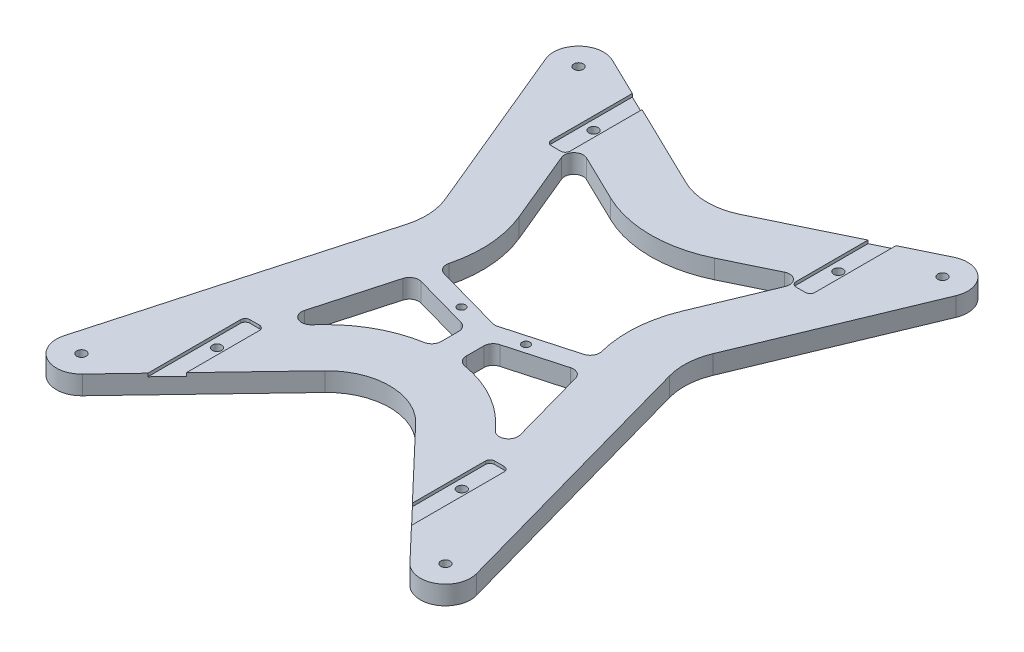
SolidWorks part; units mm, degrees
material "1060 Alloy"
ref_plane "Front Plane" through (0, 0, 0) normal (0, 0, 1) x (1, 0, 0)
ref_plane "Top Plane" through (0, 0, 0) normal (0, 1, 0) x (1, 0, 0)
ref_plane "Right Plane" through (0, 0, 0) normal (1, 0, 0) x (0, 0, -1)
sketch "Sketch1" plane through (0, 0, 0) normal (0, 1, 0) x (1, 0, 0)
  line L0 (-54.4954, 86.3958) -> (0, 60)
  line L1 (0, 60) -> (54.4954, 86.3958)
  line L2 (65.3716, 76.1292) -> (40, 15)
  line L3 (40, 15) -> (65.6883, -77.0455)
  line L4 (52.194, -84.7177) -> (0, -30)
  line L5 (0, -30) -> (-52.194, -84.7177)
  line L6 (-65.6883, -77.0455) -> (-40, 15)
  line L7 (-40, 15) -> (-65.3716, 76.1292)
  line L8 (-68.5894, 68.5894) -> (68.5894, -68.5894) construction
  line L9 (-42, 75) -> (-36, 75) construction
  line L10 (-42, 75) -> (-42, 55) construction
  line L11 (-42, 55) -> (-36, 55) construction
  line L12 (-36, 75) -> (-36, 55) construction
  line L13 (-42, 75) -> (-36, 55) construction
  line L14 (-42, 55) -> (-36, 75) construction
  line L15 (36, 75) -> (42, 75) construction
  line L16 (36, 75) -> (36, 55) construction
  line L17 (36, 55) -> (42, 55) construction
  line L18 (42, 75) -> (42, 55) construction
  line L19 (36, 75) -> (42, 55) construction
  line L20 (36, 55) -> (42, 75) construction
  line L21 (36, -45) -> (42, -45) construction
  line L22 (36, -45) -> (36, -65) construction
  line L23 (36, -65) -> (42, -65) construction
  line L24 (42, -45) -> (42, -65) construction
  line L25 (36, -45) -> (42, -65) construction
  line L26 (36, -65) -> (42, -45) construction
  line L27 (-42, -45) -> (-36, -45) construction
  line L28 (-42, -45) -> (-42, -65) construction
  line L29 (-42, -65) -> (-36, -65) construction
  line L30 (-36, -45) -> (-36, -65) construction
  line L31 (-42, -45) -> (-36, -65) construction
  line L32 (-42, -65) -> (-36, -45) construction
  line L33 (97, 40.1787) -> (40.1787, 97) construction
  line L34 (40.1787, 97) -> (-40.1787, 97) construction
  line L35 (-40.1787, 97) -> (-97, 40.1787) construction
  line L36 (-97, 40.1787) -> (-97, -40.1787) construction
  line L37 (-97, -40.1787) -> (-40.1787, -97) construction
  line L38 (-40.1787, -97) -> (40.1787, -97) construction
  line L39 (40.1787, -97) -> (97, -40.1787) construction
  line L40 (97, -40.1787) -> (97, 40.1787) construction
  line L41 (68.5894, 68.5894) -> (-68.5894, -68.5894) construction
  circle A0 centre (-57.9828, 79.196) radius 1.5
  circle A1 centre (57.9828, 79.196) radius 1.5
  circle A2 centre (-57.9828, -79.196) radius 1.5
  circle A3 centre (57.9828, -79.196) radius 1.5
  arc A4 (-54.4954, 86.3958) -> (-65.3716, 76.1292) centre (-57.9828, 79.196) ccw
  arc A5 (54.4954, 86.3958) -> (65.3716, 76.1292) centre (57.9828, 79.196) cw
  arc A6 (-65.6883, -77.0455) -> (-52.194, -84.7177) centre (-57.9828, -79.196) ccw
  arc A7 (65.6883, -77.0455) -> (52.194, -84.7177) centre (57.9828, -79.196) cw
  circle A8 centre (0, 0) radius 97 construction
  circle A9 centre (-39, 65) radius 1.5
  circle A10 centre (39, 65) radius 1.5
  circle A11 centre (39, -55) radius 1.5
  circle A12 centre (-39, -55) radius 1.5
  ellipse E0 centre (0, 15) end of major axis (0, 60) minor radius 40 construction
  dimension "D5" = 3
  dimension "D6" = 45
  dimension "D7" = 8
  dimension "D12" = 3
  dimension "D3" = 15
  dimension "D4" = 15
  dimension "D8" = 120
  dimension "D9" = 78
  dimension "D10" = 15
  dimension "D11" = 55
  dimension "D13" = 40
  dimension "D14" = 39
  dimension "D15" = 20
  dimension "D16" = 6
  dimension "D17" = 97
  dimension "D18" = 15
extrude "Boss-Extrude1" add sketch "Sketch1" along normal blind 6
fillet "Fillet1" radius 20 4 edges at (0, 3, -60) (-40, 3, -15) (0, 3, 30) (40, 3, -15)
sketch "Sketch2" plane through (0, 6, 0) normal (0, 1, 0) x (1, 0, 0)
  line L44 (-38.6591, 58.7249) -> (-26.025, 28.2848)
  line L45 (-24.5208, 3.5031) -> (-37.5911, -43.3302)
  line L46 (-37.5911, -43.3302) -> (-27.4967, -32.7477)
  line L47 (27.4967, -32.7477) -> (37.5911, -43.3302)
  line L48 (37.5911, -43.3302) -> (24.5208, 3.5031)
  line L49 (26.025, 28.2848) -> (38.6591, 58.7249)
  line L50 (38.6591, 58.7249) -> (16.5651, 48.0232)
  line L51 (-16.5651, 48.0232) -> (-38.6591, 58.7249)
  line L52 (-38.6591, 58.7249) -> (-26.025, 28.2848)
  line L53 (-24.5208, 3.5031) -> (-37.5911, -43.3302)
  line L54 (-37.5911, -43.3302) -> (-27.4967, -32.7477)
  line L55 (27.4967, -32.7477) -> (37.5911, -43.3302)
  line L56 (37.5911, -43.3302) -> (24.5208, 3.5031)
  line L57 (26.025, 28.2848) -> (38.6591, 58.7249)
  line L58 (38.6591, 58.7249) -> (16.5651, 48.0232)
  line L59 (-16.5651, 48.0232) -> (-38.6591, 58.7249)
  arc A40 (-24.5208, 3.5031) -> (-26.025, 28.2848) centre (-61.1221, 13.7179) ccw
  arc A41 (27.4967, -32.7477) -> (-27.4967, -32.7477) centre (0, -58.9762) ccw
  arc A42 (26.025, 28.2848) -> (24.5208, 3.5031) centre (61.1221, 13.7179) ccw
  arc A43 (-16.5651, 48.0232) -> (16.5651, 48.0232) centre (0, 82.2226) ccw
  arc A44 (-24.5208, 3.5031) -> (-26.025, 28.2848) centre (-61.1221, 13.7179) ccw
  arc A45 (27.4967, -32.7477) -> (-27.4967, -32.7477) centre (0, -58.9762) ccw
  arc A46 (26.025, 28.2848) -> (24.5208, 3.5031) centre (61.1221, 13.7179) ccw
  arc A47 (-16.5651, 48.0232) -> (16.5651, 48.0232) centre (0, 82.2226) ccw
  dimension "D1" = 18
extrude "Cut-Extrude1" cut sketch "Sketch2" against normal up to next
sketch "Sketch5" plane through (0, 6, 0) normal (0, 1, 0) x (1, 0, 0)
  line L0 (-25.1032, 1.416) -> (0, -5.5899)
  line L1 (-12.94, -8.43) -> (12.94, -8.43) construction
  line L2 (-12.94, -8.43) -> (-12.94, 8.43) construction
  line L3 (-12.94, 8.43) -> (12.94, 8.43) construction
  line L4 (12.94, -8.43) -> (12.94, 8.43) construction
  line L5 (-12.94, -8.43) -> (12.94, 8.43) construction
  line L6 (-12.94, 8.43) -> (12.94, -8.43) construction
  line L7 (-24.5208, 3.5031) -> (-37.5911, -43.3302) construction
  line L8 (0, -5.5899) -> (25.1032, 1.416)
  line L9 (37.5911, -43.3302) -> (24.5208, 3.5031) construction
  line L10 (25.1032, 1.416) -> (26.7161, -4.3632)
  line L11 (26.7161, -4.3632) -> (4, -10.7029)
  line L12 (4, -10.7029) -> (4, -21.1873)
  line L13 (-4, -21.1873) -> (-4, -10.7029)
  line L14 (-4, -10.7029) -> (-26.7161, -4.3632)
  line L15 (-26.7161, -4.3632) -> (-25.1032, 1.416)
  circle A0 centre (-10.3, -5.83) radius 1.25
  circle A1 centre (10.3, -5.83) radius 1.25
  arc A2 (27.4967, -32.7477) -> (-27.4967, -32.7477) centre (0, -58.9762) ccw construction
  arc A3 (4, -21.1873) -> (-4, -21.1873) centre (0, -58.9762) ccw
  point P0 (0, 0)
  dimension "D3" = 2.5
  dimension "D1" = 16.86
  dimension "D2" = 25.88
  dimension "D4" = 20.6
  dimension "D5" = 2.64
  dimension "D6" = 2.6
  dimension "D7" = 6
  dimension "D8" = 3
  dimension "D9" = 8
extrude "Boss-Extrude2" add sketch "Sketch5" against normal up to surface (6 mm away) up to face at (0, 0, -11.095)
fillet "Fillet2" radius 3 13 edges at (37.5911, 3, 43.3302) (-37.5911, 3, 43.3302) (38.6591, 3, -58.7249) (-38.6591, 3, -58.7249) (25.1032, 3, -1.416) (-25.1032, 3, -1.416) (0, 3, 5.5899) (26.7161, 3, 4.3632) (4, 3, 10.7029) (4, 3, 21.1873) (-4, 3, 21.1873) (-4, 3, 10.7029) (-26.7161, 3, 4.3632)
sketch "Sketch6" plane through (0, 6, 0) normal (0, 1, 0) x (1, 0, 0)
  line L0 (-8.7185, 64.223) -> (-54.4954, 86.3958) construction
  line L1 (-42, -43) -> (-36, -43)
  line L2 (-42, -43) -> (-42, -74.0308)
  line L3 (-42, -74.0308) -> (-36, -74.0308)
  line L4 (-36, -43) -> (-36, -74.0308)
  line L5 (36, -43) -> (42, -43)
  line L6 (36, -43) -> (36, -74.0308)
  line L7 (36, -74.0308) -> (42, -74.0308)
  line L8 (42, -43) -> (42, -74.0308)
  line L9 (36, 53) -> (42, 53)
  line L10 (36, 53) -> (36, 80.3435)
  line L11 (36, 80.3435) -> (42, 80.3435)
  line L12 (42, 53) -> (42, 80.3435)
  line L13 (-42, 53) -> (-36, 53)
  line L14 (-42, 53) -> (-42, 80.3435)
  line L15 (-42, 80.3435) -> (-36, 80.3435)
  line L16 (-36, 53) -> (-36, 80.3435)
  line L17 (54.4954, 86.3958) -> (8.7185, 64.223) construction
  line L18 (14.4719, -45.1717) -> (52.194, -84.7177) construction
  line L19 (-52.194, -84.7177) -> (-14.4719, -45.1717) construction
  circle A0 centre (-39, -55) radius 1.5 construction
  circle A1 centre (39, -55) radius 1.5 construction
  circle A2 centre (-39, 65) radius 1.5 construction
  dimension "D2" = 3
  dimension "D3" = 3
  dimension "D5" = 12
  dimension "D1" = 6
  dimension "D4" = 12
extrude "Cut-Extrude2" cut sketch "Sketch6" against normal blind 1
fillet "Fillet3" radius 1.5 8 edges at (-36, 5.5, -53) (-42, 5.5, -53) (36, 5.5, -53) (42, 5.5, -53) (36, 5.5, 43) (42, 5.5, 43) (-36, 5.5, 43) (-42, 5.5, 43)
equation "\"D14@Sketch1\"=\"D9@Sketch1\"/2"
